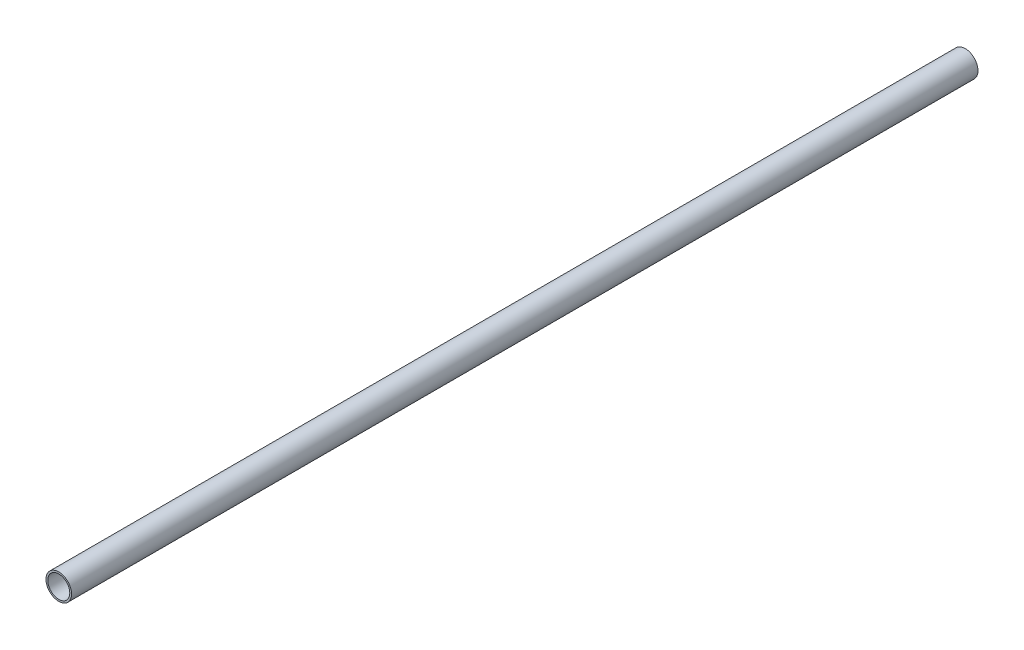
SolidWorks part; units mm, degrees
material "6063-T6, Rod (SS)"
ref_plane "Front Plane" through (0, 0, 0) normal (0, 0, 1) x (1, 0, 0)
ref_plane "Top Plane" through (0, 0, 0) normal (0, 1, 0) x (1, 0, 0)
ref_plane "Right Plane" through (0, 0, 0) normal (1, 0, 0) x (0, 0, -1)
sketch "Sketch1" plane through (0, 0, 0) normal (0, 0, 1) x (1, 0, 0)
  circle A0 centre (0, 0) radius 6.35
  circle A1 centre (0, 0) radius 5.461
  dimension "D1" = 12.7
  dimension "D2" = 10.922
extrude "Boss-Extrude1" add sketch "Sketch1" along normal blind 450
